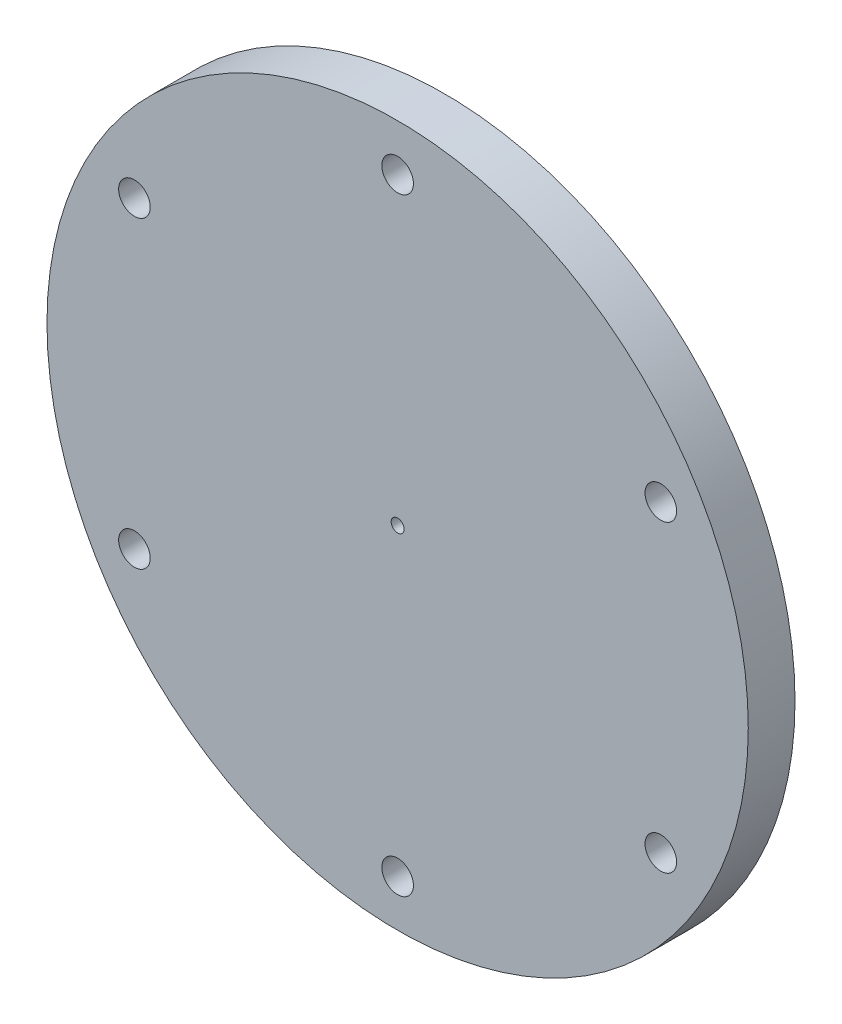
SolidWorks part; units mm, degrees
ref_plane "Front Plane" through (0, 0, 0) normal (0, 0, 1) x (1, 0, 0)
ref_plane "Top Plane" through (0, 0, 0) normal (0, 1, 0) x (1, 0, 0)
ref_plane "Right Plane" through (0, 0, 0) normal (1, 0, 0) x (0, 0, -1)
sketch "Sketch1" plane through (0, 0, 0) normal (0, 0, 1) x (1, 0, 0)
  circle A0 centre (0, 0) radius 37.5
  dimension "D1" = 75
extrude "Boss-Extrude1" add sketch "Sketch1" along normal blind 5
sketch "Sketch2" plane through (0, 0, 0) normal (0, 0, -1) x (-1, 0, 0)
  circle A0 centre (0, 0) radius 0.693
  dimension "D1" = 1.386
extrude "Cut-Extrude1" cut sketch "Sketch2" against normal through all
sketch "Sketch3" plane through (0, 0, 0) normal (0, 0, -1) x (-1, 0, 0)
  line L0 (0, 37.5) -> (0, -37.5) construction
  circle A0 centre (0, 0) radius 37.5 construction
  circle A1 centre (0, 32.5) radius 1.69
  circle A2 centre (28.1458, 16.25) radius 1.69
  circle A3 centre (28.1458, -16.25) radius 1.69
  circle A4 centre (0, -32.5) radius 1.69
  circle A5 centre (-28.1458, -16.25) radius 1.69
  circle A6 centre (-28.1458, 16.25) radius 1.69
  dimension "D1" = 3.38
  dimension "D2" = 5
  dimension "D3" = 6
extrude "Cut-Extrude2" cut sketch "Sketch3" against normal through all
